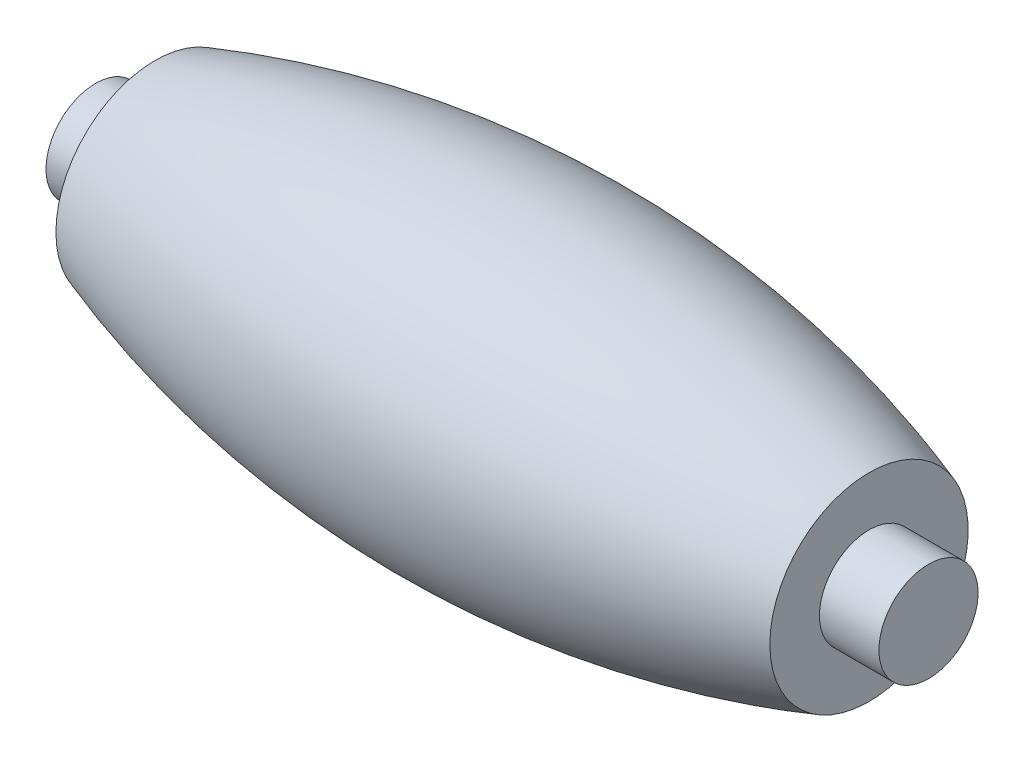
SolidWorks part; units mm, degrees
ref_plane "Front Plane" through (0, 0, 0) normal (0, 0, 1) x (1, 0, 0)
ref_plane "Top Plane" through (0, 0, 0) normal (0, 1, 0) x (1, 0, 0)
ref_plane "Right Plane" through (0, 0, 0) normal (1, 0, 0) x (0, 0, -1)
sketch "Sketch2" plane through (0, 0, 0) normal (0, 1, 0) x (1, 0, 0)
  line L0 (0, 0) -> (42, 0) construction
  line L1 (0, 0) -> (0, 2.5)
  line L2 (0, 2.5) -> (3, 2.5)
  line L5 (3, 2.5) -> (3, 5)
  line L6 (42, 0) -> (42, 2.5)
  line L7 (42, 2.5) -> (39, 2.5)
  line L8 (39, 2.5) -> (39, 5)
  line L9 (0, 0) -> (42, 0)
  arc A0 (3, 5) -> (39, 5) centre (21, -47.3353) cw
revolve "Revolve1" add sketch "Sketch2" angle 360 about L0
